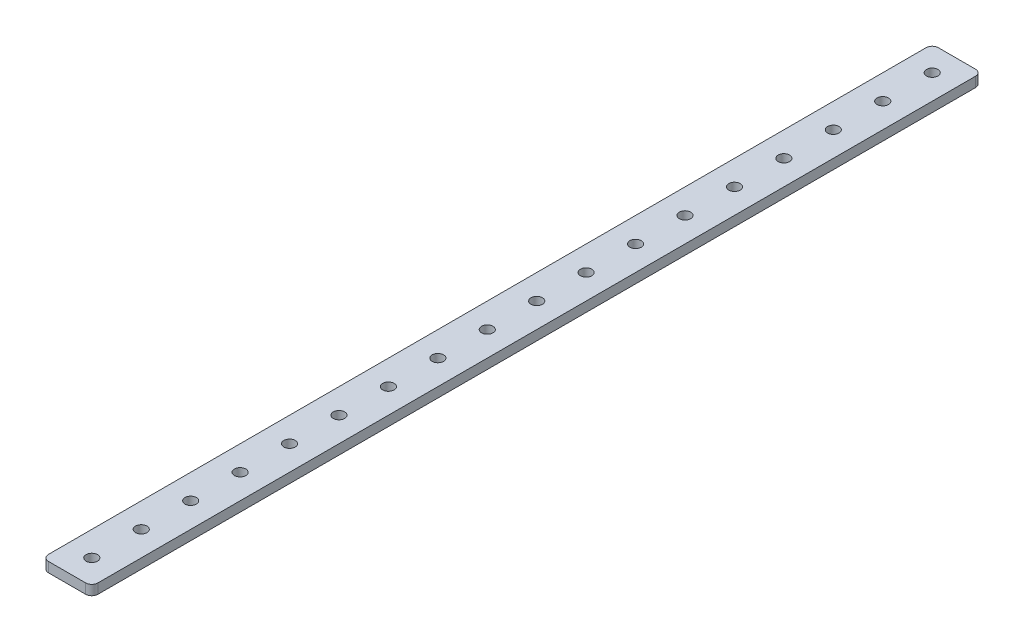
SolidWorks part; units mm, degrees
material "2024 Alloy"
ref_plane "Front Plane" through (0, 0, 0) normal (0, 0, 1) x (1, 0, 0)
ref_plane "Top Plane" through (0, 0, 0) normal (0, 1, 0) x (1, 0, 0)
ref_plane "Right Plane" through (0, 0, 0) normal (1, 0, 0) x (0, 0, -1)
ref_plane "Plane1" through (0, 3.2, 0) normal (0, 1, 0) x (1, 0, 0)
sketch "Sketch1" plane through (0, 3.2, 0) normal (0, 1, 0) x (1, 0, 0)
  line L0 (6, 288) -> (-6, 288)
  line L1 (-8, 286) -> (-8, 2)
  line L2 (-6, 0) -> (6, 0)
  line L3 (8, 2) -> (8, 286)
  circle A0 centre (0, 8) radius 1.85
  circle A1 centre (0, 280) radius 1.85
  circle A2 centre (0, 264) radius 1.85
  circle A3 centre (0, 248) radius 1.85
  circle A4 centre (0, 232) radius 1.85
  circle A5 centre (0, 216) radius 1.85
  circle A6 centre (0, 200) radius 1.85
  circle A7 centre (0, 184) radius 1.85
  circle A8 centre (0, 168) radius 1.85
  circle A9 centre (0, 152) radius 1.85
  circle A10 centre (0, 136) radius 1.85
  circle A11 centre (0, 120) radius 1.85
  circle A12 centre (0, 104) radius 1.85
  circle A13 centre (0, 88) radius 1.85
  circle A14 centre (0, 72) radius 1.85
  circle A15 centre (0, 56) radius 1.85
  circle A16 centre (0, 40) radius 1.85
  circle A17 centre (0, 24) radius 1.85
  arc A18 (8, 286) -> (6, 288) centre (6, 286) ccw
  arc A19 (-6, 288) -> (-8, 286) centre (-6, 286) ccw
  arc A20 (-8, 2) -> (-6, 0) centre (-6, 2) ccw
  arc A21 (6, 0) -> (8, 2) centre (6, 2) ccw
extrude "Boss-Extrude1" add sketch "Sketch1" against normal blind 3.2
